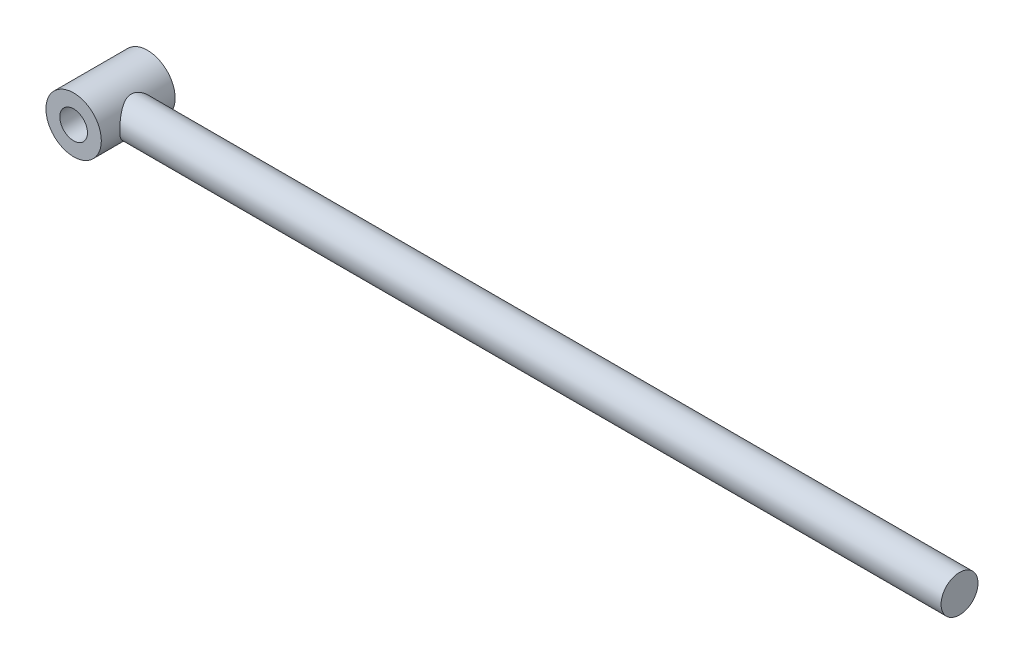
SolidWorks part; units mm, degrees
ref_plane "Front Plane" through (0, 0, 0) normal (0, 0, 1) x (1, 0, 0)
ref_plane "Top Plane" through (0, 0, 0) normal (0, 1, 0) x (1, 0, 0)
ref_plane "Right Plane" through (0, 0, 0) normal (1, 0, 0) x (0, 0, -1)
sketch "Sketch1" plane through (0, 0, 0) normal (0, 0, 1) x (1, 0, 0)
  circle A0 centre (0, 0) radius 30
  circle A1 centre (0, 0) radius 15
  dimension "D1" = 30
  dimension "D2" = 15
extrude "Boss-Extrude1" add sketch "Sketch1" along normal mid plane 80
ref_plane "Plane1" through (20, 0, 0) normal (1, 0, 0) x (0, 0, -1)
sketch "Sketch2" plane through (20, 0, 0) normal (1, 0, 0) x (0, 0, -1)
  circle A0 centre (0, 0) radius 20
  dimension "D1" = 40
extrude "Boss-Extrude2" add sketch "Sketch2" along normal blind 900
